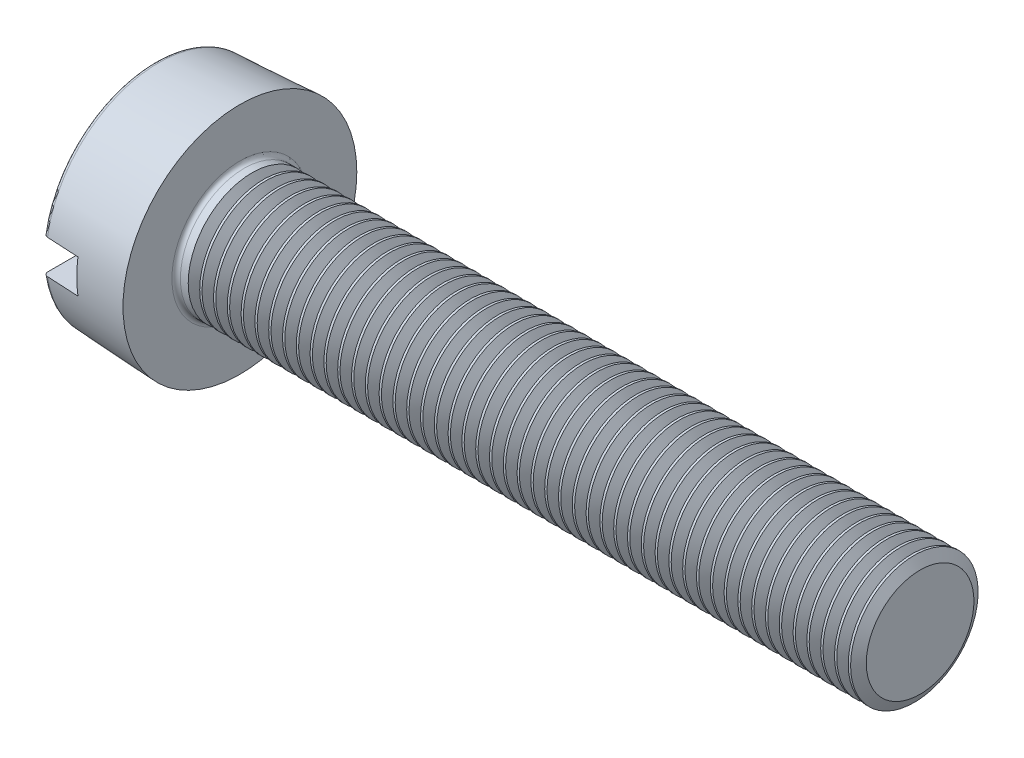
SolidWorks part; units mm, degrees
ref_plane "Front" through (0, 0, 0) normal (0, 0, 1) x (1, 0, 0)
ref_plane "Top" through (0, 0, 0) normal (0, 1, 0) x (1, 0, 0)
ref_plane "Right" through (0, 0, 0) normal (1, 0, 0) x (0, 0, -1)
ref_plane "Plane1" through (2, 0, 0) normal (1, 0, 0) x (0, 0, -1)
sketch "Sketch2" plane through (2, 0, 0) normal (1, 0, 0) x (0, 0, -1)
  circle A0 centre (0, 0) radius 2.75
  dimension "dk" = 5.5
extrude "BaseHead" add sketch "Sketch2" against normal blind 2 draft 3
sketch "Sketch3" plane through (2, -1.1101, -1.3544) normal (1, 0, 0) x (0, 0, -1)
  line L0 (-1.3544, 1.1101) -> (-0.3544, 1.1101) construction
  circle A0 centre (-1.3544, 1.1101) radius 1.5
  circle A1 centre (-1.3544, 1.1101) radius 2.75 construction
  dimension "d" = 3
  dimension "a" = 1
extrude "BaseBody" add sketch "Sketch3" along normal blind 16
cosmetic thread "ThreadCosmetic1" [suppressed] parameters "D1"=16, "D2"=2.459
sketch "Sketch4" plane through (-1.9, -1.9, 0) normal (0, 0, 1) x (0, 1, 0)
  line L1 (1.5, -1.9) -> (2.3, -1.9)
  line L2 (1.5, -1.9) -> (1.5, -2.75)
  line L3 (1.5, -2.75) -> (2.3, -2.75)
  line L4 (2.3, -1.9) -> (2.3, -2.75)
  line L5 (4.5452, -1.9) -> (-0.7452, -1.9) construction
  dimension "n" = 0.8
  dimension "m" = 0.4
  dimension "t" = 0.85
extrude "Slot" cut sketch "Sketch4" against normal through all and the other way through all
fillet "HeadFillet" radius 0.1 3 edges at (2, 0, -1.5) (0, -2.6452, 0) (0, 2.6452, 0)
sketch "Sketch1" plane through (0, 0, 0) normal (0, 0, 1) x (1, 0, 0)
  line L0 (5.5483, 0) -> (-2.9147, 0) construction
  line L1 (2, 6.2295) -> (-7, 6.2295)
  line L2 (2, 6.2295) -> (2, 1.2295)
  line L3 (2, 1.2295) -> (-8.25, 1.2295)
  line L8 (-7, 1.5) -> (-8.25, 1.2295)
  line L9 (-7, 6.2295) -> (-7, 1.5)
  line L10 (2, -2.75) -> (2, 2.75) construction
  line L11 (18, -1.5) -> (18, 1.5) construction
  line L12 (18, 1.5) -> (2.1, 1.5) construction
  dimension "b1" = 2.459
  dimension "b" = 25
  dimension "x" = 1.25
  dimension "dd" = 5
sketch "Sketch5" plane through (0, 0, 0) normal (0, 0, 1) x (1, 0, 0)
  line L0 (18.1352, 1.5) -> (18.1352, 1.7705)
  line L1 (18.1352, 1.7705) -> (17.8647, 1.7705)
  line L2 (17.8647, 1.7705) -> (17.8647, 1.5)
  line L3 (17.8647, 1.5) -> (18, 1.2657)
  line L4 (18, 1.2657) -> (18.1352, 1.5)
  line L5 (18, -1.5) -> (18, 1.5) construction
  line L6 (0, 0) -> (15.9087, 0) construction
  dimension "D1" = 3
  dimension "D2" = 0.2705
revolve "Cut-Revolve10" cut sketch "Sketch5" angle 360 about L6
pattern_linear "LPattern10" count 49 spacing 0.3246 along (-1, 0, 0) of "Cut-Revolve10"
equation "\"m@Sketch4\" = \"n@Sketch4\" / 2"
equation "\"D1@Plane1\"=\"k@BaseHead\""
equation "\"D1@Sketch5\" = \"d@Sketch3\""
equation "\"D2@Sketch5\" =  ( \"d@Sketch3\" - \"D2@ThreadCosmetic1\" )  / 2"
equation "\"D3@LPattern10\" = \"D2@Sketch5\" * 1.2"
equation "\"D1@LPattern10\" = \"D1@ThreadCosmetic1\" / \"D3@LPattern10\""
